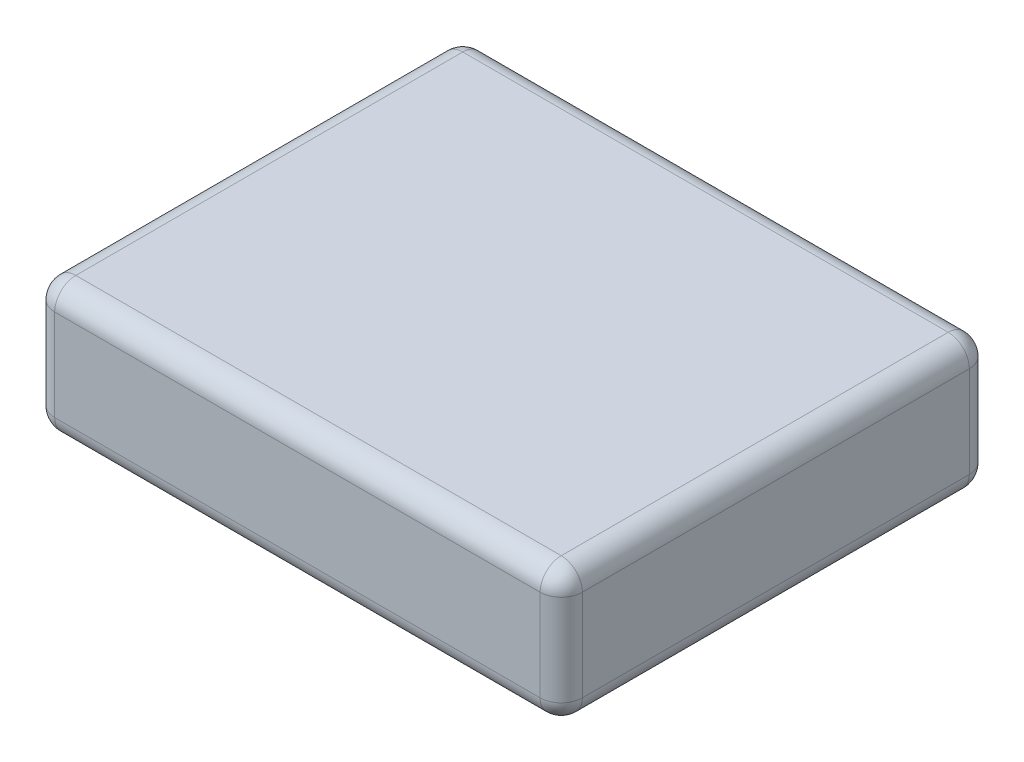
SolidWorks part; units mm, degrees
ref_plane "Front Plane" through (0, 0, 0) normal (0, 0, 1) x (1, 0, 0)
ref_plane "Top Plane" through (0, 0, 0) normal (0, 1, 0) x (1, 0, 0)
ref_plane "Right Plane" through (0, 0, 0) normal (1, 0, 0) x (0, 0, -1)
sketch "Sketch1" plane through (0, 0, 0) normal (0, 1, 0) x (1, 0, 0)
  line L0 (0, 44.6163) -> (0, -79.7242) construction
  line L1 (-37.5, 30.5) -> (37.5, 30.5)
  line L2 (-37.5, 30.5) -> (-37.5, -30.5)
  line L3 (-37.5, -30.5) -> (37.5, -30.5)
  line L4 (37.5, 30.5) -> (37.5, -30.5)
  line L5 (-74.8969, 0) -> (90.2566, 0) construction
  dimension "D1" = 61
  dimension "D2" = 75
extrude "Boss-Extrude1" add sketch "Sketch1" along normal blind 19
fillet "Fillet1" radius 3 12 edges at (0, 0, -30.5) (0, 0, 30.5) (0, 19, 30.5) (0, 19, -30.5) (37.5, 19, 0) (37.5, 0, 0) (-37.5, 0, 0) (-37.5, 19, 0) (-37.5, 9.5, -30.5) (-37.5, 9.5, 30.5) (37.5, 9.5, 30.5) (37.5, 9.5, -30.5)
